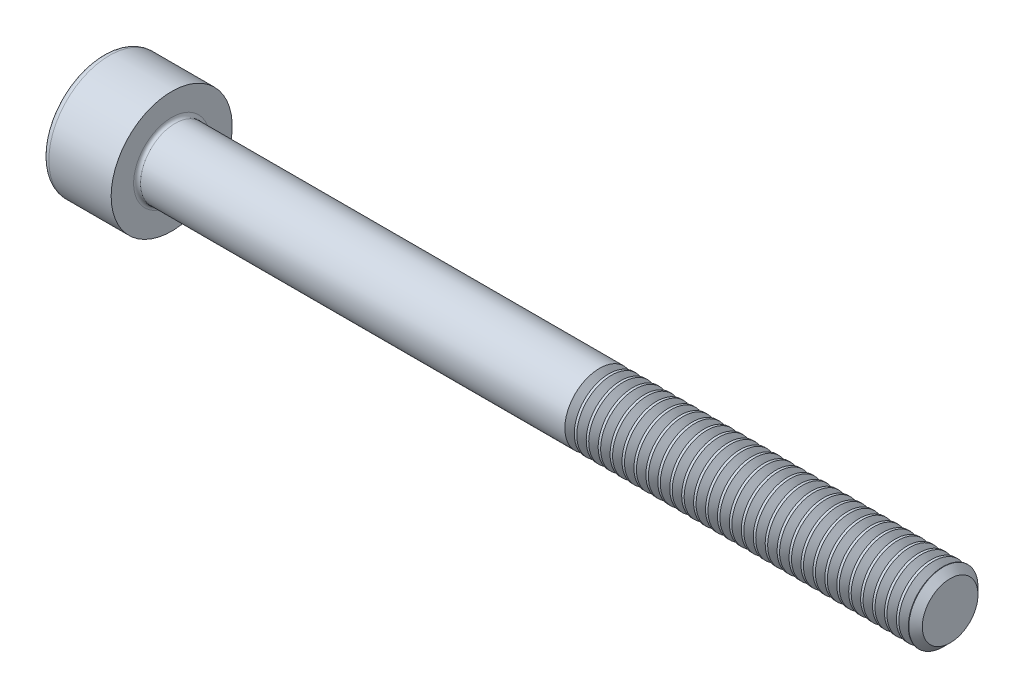
SolidWorks part; units mm, degrees
revolve "Base-Revolve" add sketch "BodySke"
sketch "BodySke" plane through (0, 0, 0) normal (0, 0, 1) x (1, 0, 0)
  line L0 (0, 0) -> (0, 3.5)
  line L1 (0, 3.5) -> (4, 3.5)
  line L2 (4, 3.5) -> (4, 2)
  line L3 (4, 2) -> (48.61, 2)
  line L4 (49, 1.61) -> (49, 0)
  line L5 (49, 0) -> (0, 0)
  line L6 (-31.75, 0) -> (127, 0) construction
  line L8 (49, 1.61) -> (48.61, 2)
  line L10 (49, -1.61) -> (48.61, -2) construction
  line L11 (4.7, 9.525) -> (4.7, 3.175) construction
  line L12 (29, 9.525) -> (29, 3.175) construction
  line L13 (-11, 9.525) -> (-11, 3.175) construction
cosmetic thread "ThreadCosmetic" [suppressed]
fillet "Fillet1" radius 0.2 1 edges at (4, 0, 2)
fillet "Fillet2" radius 0.4 1 edges at (0, 0, 3.5)
ref_plane "Plane1" through (0, 0, 0) normal (0, 0, 1) x (1, 0, 0)
ref_plane "Plane2" through (0, 0, 0) normal (0, 1, 0) x (1, 0, 0)
ref_plane "Plane3" through (0, 0, 0) normal (1, 0, 0) x (0, 0, -1)
sketch "Sketch2" plane through (0, 0, 0) normal (0, 0, 1) x (1, 0, 0)
  line L0 (0, 1.51) -> (2, 1.51)
  line L1 (2, 1.51) -> (2.8718, 0)
  line L2 (-31.75, 0) -> (127, 0) construction
  line L3 (2.8718, 0) -> (0, 0)
  line L4 (0, 0) -> (0, 1.51)
  line L6 (0, 0) -> (47.625, 0) construction
revolve "Hex-PreBroach" cut sketch "Sketch2" angle 360 about L6
sketch "Sketch3" plane through (0, 0, 0) normal (-1, 0, 0) x (0, 0.5, 0.866)
  line L0 (0.8718, 1.51) -> (-0.8718, 1.51)
  line L1 (-0.8718, 1.51) -> (-1.7436, 0)
  line L2 (0.8718, 1.51) -> (1.7436, 0)
  line L3 (0.8718, -1.51) -> (1.7436, 0)
  line L4 (0.8718, -1.51) -> (-0.8718, -1.51)
  line L5 (-0.8718, -1.51) -> (-1.7436, 0)
extrude "Hex" cut sketch "Sketch3" against normal blind 2
sketch "ThdSchSke" plane through (0, 0, 0) normal (0, 0, 1) x (1, 0, 0)
  line L0 (29, -1.61) -> (28.7269, -2)
  line L1 (29, -1.61) -> (29.2731, -2)
  line L2 (29.2731, -2) -> (29.2731, -2.5)
  line L3 (-3.175, 0) -> (5.1513, 0) construction
  line L4 (0, 3.1) -> (0, -3.1) construction
  line L5 (29.2731, -2.5) -> (28.7269, -2.5)
  line L6 (28.7269, -2.5) -> (28.7269, -2)
revolve "ThreadSchematic" cut sketch "ThdSchSke" angle 360 about L3
pattern_linear "ThdSchPat" count 29 spacing 0.6897 along (1, 0, 0) of "ThreadSchematic"
equation "\"D2@Sketch3\" = \"Hex_size@Sketch3\" / 2"
equation "\"D1@Sketch3\" = \"Hex_size@Sketch3\" / 2"
equation "\"D1@Sketch2\" = \"Hex_size@Sketch3\" / 2"
equation "\"Thread_minor@ThreadCosmetic\"  =  \"Minor_dia@BodySke\""
equation "\"Depth@Sketch2\" =  \"Key_eng@Hex\""
equation "\"Thread_length@ThreadCosmetic\" = ((sgn( (\"Length@BodySke\" - \"Advance@BodySke\" * 3.0) - \"Thread_nom@BodySke\" )-1)*( (\"Length@BodySke\" - \"Advance@BodySke\" * 3.0) - \"Thread_nom@BodySke\" ))/-2+ \"Thread_nom@BodySke\""
equation "\"Thread_minor@ThdSchSke\" = \"Minor_dia@BodySke\""
equation "\"Diameter@ThdSchSke\" = \"Diameter@BodySke\""
equation "\"Overcut@ThdSchSke\" = \"Diameter@BodySke\" * 1.25"
equation "\"Start@ThdSchSke\" = \"Head_ht@BodySke\" + \"Length@BodySke\" - \"Thread_length@ThreadCosmetic\"  '---Non-countersunk---"
equation "\"Num_threads@ThdSchPat\" = int( \"Thread_length@ThreadCosmetic\" / \"Advance@BodySke\" + 0.999 )  + 1"
equation "\"Advance@ThdSchPat\" = \"Thread_length@ThreadCosmetic\" /  (\"Num_threads@ThdSchPat\" - 1) 'relax it"
equation "\"Num_threads@ThdSchPat\" = \"Num_threads@ThdSchPat\" - sgn( \"Num_threads@ThdSchPat\" - 1) '---chamfered tips only---"
